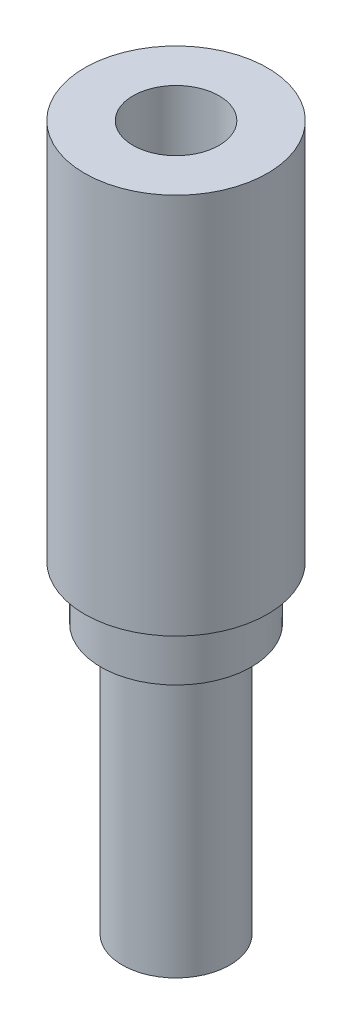
SolidWorks part; units mm, degrees
material "Plain Carbon Steel"
ref_plane "Front Plane" through (0, 0, 0) normal (0, 0, 1) x (1, 0, 0)
ref_plane "Top Plane" through (0, 0, 0) normal (0, 1, 0) x (1, 0, 0)
ref_plane "Right Plane" through (0, 0, 0) normal (1, 0, 0) x (0, 0, -1)
sketch "Sketch1" plane through (0, 0, 0) normal (0, 1, 0) x (1, 0, 0)
  circle A0 centre (0, 0) radius 8.5
  dimension "D1" = 17
extrude "Boss-Extrude1" add sketch "Sketch1" along normal blind 35.5
sketch "Sketch2" plane through (0, 35.5, 0) normal (0, 1, 0) x (1, 0, 0)
  circle A0 centre (0, 0) radius 4
  dimension "D1" = 8
sketch "Sketch3" plane through (0, 0, 0) normal (0, -1, 0) x (-1, 0, 0)
  circle A0 centre (0, 0) radius 7
  dimension "D1" = 14
extrude "Boss-Extrude2" add sketch "Sketch3" along normal blind 5
sketch "Sketch5" plane through (0, -5, 0) normal (0, -1, 0) x (-1, 0, 0)
  circle A0 centre (0, 0) radius 5
  dimension "D1" = 10
extrude "Boss-Extrude3" add sketch "Sketch5" along normal blind 25
extrude "Cut-Extrude1" cut sketch "Sketch2" against normal blind 17
